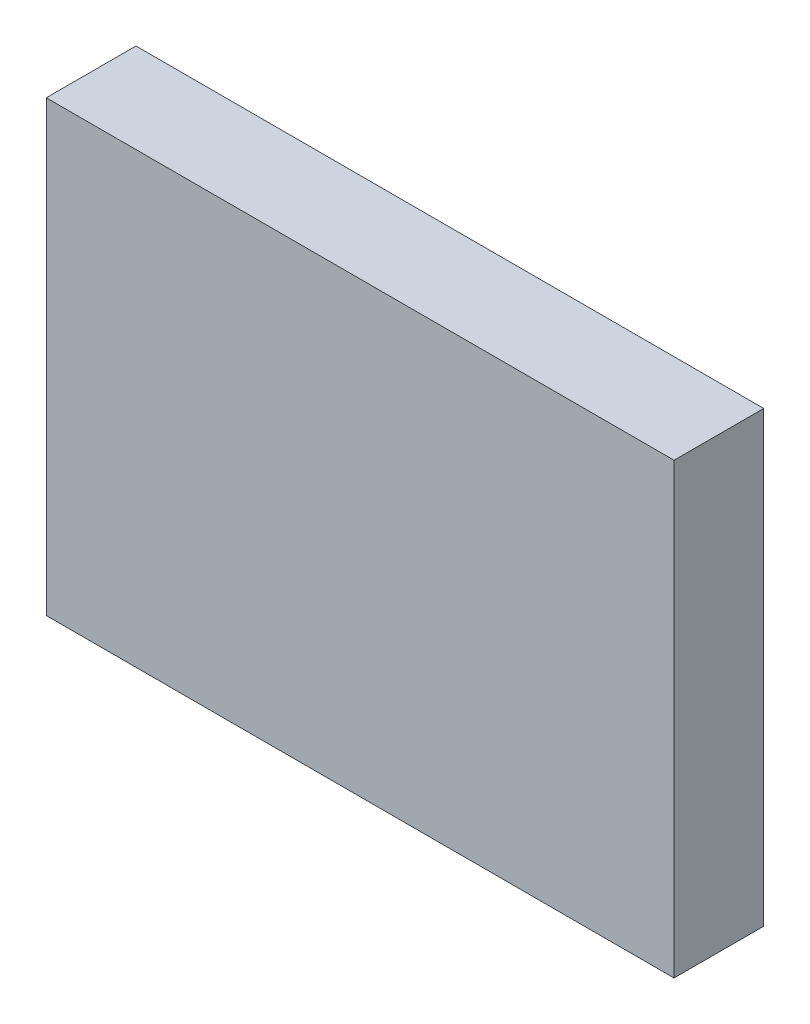
SolidWorks part; units mm, degrees
ref_plane "Front Plane" through (0, 0, 0) normal (0, 0, 1) x (1, 0, 0)
ref_plane "Top Plane" through (0, 0, 0) normal (0, 1, 0) x (1, 0, 0)
ref_plane "Right Plane" through (0, 0, 0) normal (1, 0, 0) x (0, 0, -1)
sketch "Sketch2" plane through (0, 0, 0) normal (0, 0, 1) x (1, 0, 0)
  line L0 (0, 0) -> (0, 20)
  line L1 (0, 20) -> (28, 20)
  line L2 (28, 20) -> (28, 0)
  line L3 (28, 0) -> (0, 0)
  dimension "D1" = 28
  dimension "D2" = 20
extrude "Boss-Extrude1" add sketch "Sketch2" along normal blind 4 contours L3 L0 L1 L2
